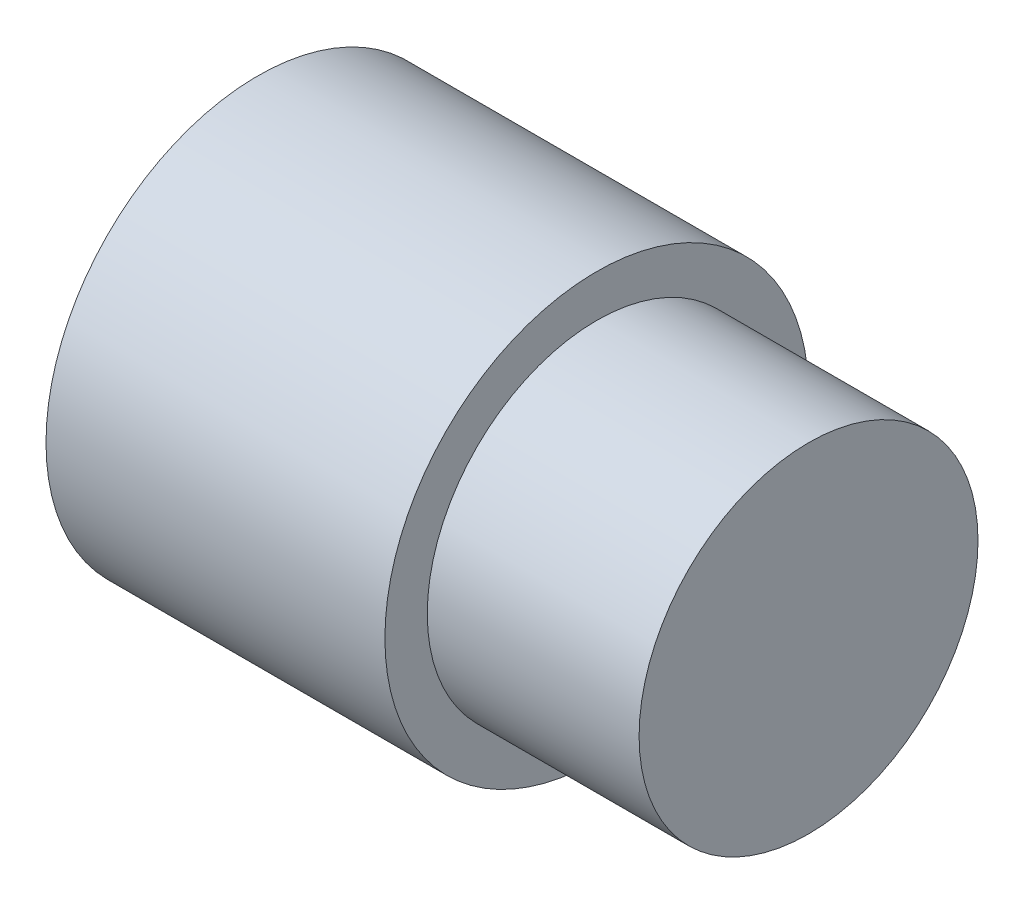
SolidWorks part; units mm, degrees
ref_plane "Front Plane" through (0, 0, 0) normal (0, 0, 1) x (1, 0, 0)
ref_plane "Top Plane" through (0, 0, 0) normal (0, 1, 0) x (1, 0, 0)
ref_plane "Right Plane" through (0, 0, 0) normal (1, 0, 0) x (0, 0, -1)
sketch "Sketch1" plane through (0, 0, 0) normal (0, 1, 0) x (1, 0, 0)
  line L0 (-47.7477, 0) -> (36.1261, 0) construction
  line L1 (25, 0) -> (25, 20)
  line L2 (25, 20) -> (0, 20)
  line L3 (0, 20) -> (0, 25)
  line L4 (0, 25) -> (-40, 25)
  line L5 (-40, 25) -> (-40, 0)
  line L6 (25, 0) -> (-40, 0)
  dimension "D1" = 25
  dimension "D2" = 5
  dimension "D3" = 40
  dimension "D4" = 65
revolve "Revolve1" add sketch "Sketch1" angle 360 about L0
